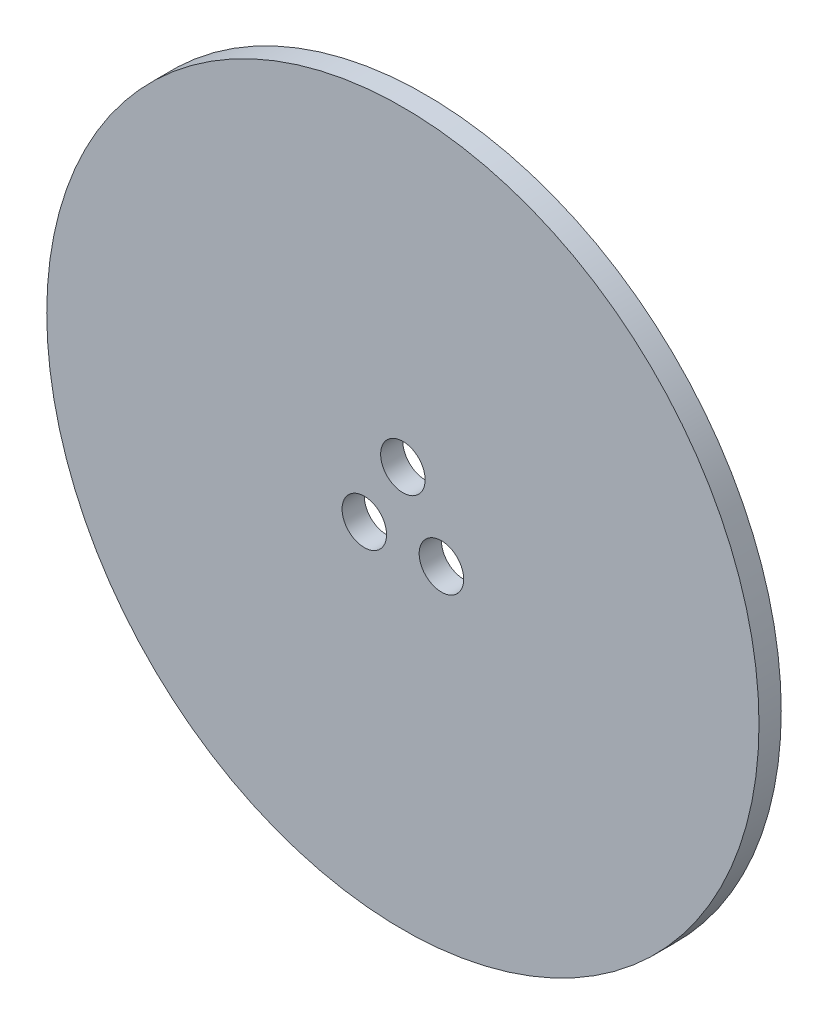
SolidWorks part; units mm, degrees
material "Pine"
ref_plane "Front Plane" through (0, 0, 0) normal (0, 0, 1) x (1, 0, 0)
ref_plane "Top Plane" through (0, 0, 0) normal (0, 1, 0) x (1, 0, 0)
ref_plane "Right Plane" through (0, 0, 0) normal (1, 0, 0) x (0, 0, -1)
sketch "Sketch1" plane through (0, 0, 0) normal (0, 0, 1) x (1, 0, 0)
  circle A0 centre (0, 0) radius 50.8
  dimension "D1" = 101.6
extrude "Boss-Extrude1" add sketch "Sketch1" along normal blind 3.175
sketch "Sketch2" plane through (0, 0, 3.175) normal (0, 0, 1) x (1, 0, 0)
  circle A0 centre (0, 0) radius 6.35 construction
  circle A1 centre (0, 6.35) radius 3.175
  circle A2 centre (5.4993, -3.175) radius 3.175
  circle A3 centre (-5.4993, -3.175) radius 3.175
  point P12 (0, 0)
  dimension "D1" = 12.7
  dimension "D2" = 6.35
  dimension "D3" = 3
extrude "Cut-Extrude1" cut sketch "Sketch2" against normal up to surface (3.175 mm away) up to face at (50.8, 0, 0)
